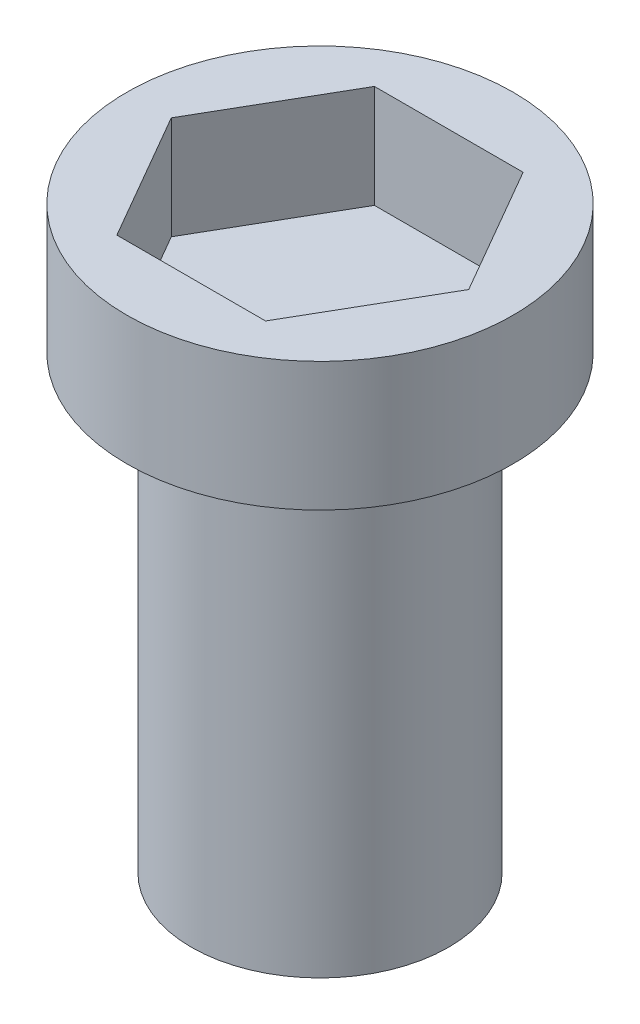
SolidWorks part; units mm, degrees
ref_plane "Front Plane" through (0, 0, 0) normal (0, 0, 1) x (1, 0, 0)
ref_plane "Top Plane" through (0, 0, 0) normal (0, 1, 0) x (1, 0, 0)
ref_plane "Right Plane" through (0, 0, 0) normal (1, 0, 0) x (0, 0, -1)
sketch "Sketch1" plane through (0, 0, 0) normal (0, 1, 0) x (1, 0, 0)
  circle A0 centre (0, 0) radius 10
  dimension "D1" = 20
extrude "Boss-Extrude1" add sketch "Sketch1" along normal blind 35
sketch "Sketch2" plane through (0, 35, 0) normal (0, 1, 0) x (1, 0, 0)
  line L1 (11.547, 0) -> (5.7735, 10)
  line L2 (5.7735, 10) -> (-5.7735, 10)
  line L3 (-5.7735, 10) -> (-11.547, 0)
  line L4 (-11.547, 0) -> (-5.7735, -10)
  line L5 (-5.7735, -10) -> (5.7735, -10)
  line L6 (5.7735, -10) -> (11.547, 0)
  circle A0 centre (0, 0) radius 15
  circle A1 centre (0, 0) radius 10 construction
  point P3 (0, 0)
  dimension "D1" = 20
  dimension "D2" = 30
extrude "Boss-Extrude2" add sketch "Sketch2" along normal blind 10 separate body
sketch "Sketch3" plane through (0, 35, 0) normal (0, 1, 0) x (1, 0, 0)
  line L1 (11.547, 0) -> (5.7735, 10)
  line L2 (5.7735, 10) -> (-5.7735, 10)
  line L3 (-5.7735, 10) -> (-11.547, 0)
  line L4 (-11.547, 0) -> (-5.7735, -10)
  line L5 (-5.7735, -10) -> (5.7735, -10)
  line L6 (5.7735, -10) -> (11.547, 0)
  circle A0 centre (0, 0) radius 10 construction
  point P1 (0, 0)
  point P10 (11.547, 0)
extrude "Boss-Extrude3" add sketch "Sketch3" along normal blind 2
